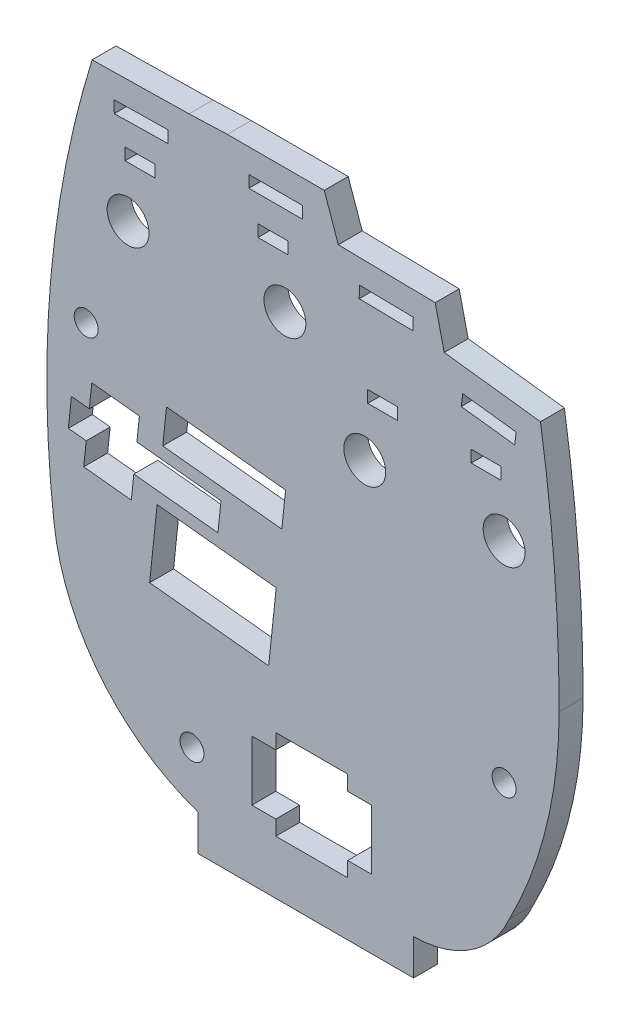
SolidWorks part; units mm, degrees
ref_plane "Front Plane" through (0, 0, 0) normal (0, 0, 1) x (1, 0, 0)
ref_plane "Top Plane" through (0, 0, 0) normal (0, 1, 0) x (1, 0, 0)
ref_plane "Right Plane" through (0, 0, 0) normal (1, 0, 0) x (0, 0, -1)
sketch "Sketch1" plane through (0, 0, 0) normal (0, 0, 1) x (1, 0, 0)
  line L0 (-4.5, 78.51) -> (-4.5, 76.51)
  line L1 (4.5, 78.51) -> (-4.5, 78.51)
  line L2 (-4.5, 76.51) -> (4.5, 76.51)
  line L3 (4.5, 76.51) -> (4.5, 78.51)
  line L4 (-4, -2.5) -> (0, -2.5)
  line L5 (0, 0) -> (18.54, 0) construction
  line L6 (0, 0) -> (0, 82.51) construction
  line L7 (12, 0) -> (0, 0)
  line L8 (0, 0) -> (-22.59, 0) construction
  line L9 (32.6473, 57.3216) -> (37.6473, 57.3216)
  line L10 (-12.9786, -18) -> (-12.9786, -24)
  line L11 (32.6473, 55.3216) -> (37.6473, 55.3216)
  line L12 (37.6473, 55.3216) -> (37.6473, 57.3216)
  line L13 (32.6473, 57.3216) -> (32.6473, 55.3216)
  line L14 (-27.02, 78.0626) -> (-18.0213, 78.2186)
  line L15 (-27.02, 78.0626) -> (-26.9853, 76.0629)
  line L16 (-26.9853, 76.0629) -> (-17.9866, 76.2189)
  line L17 (-17.9866, 76.2189) -> (-18.0213, 78.2186)
  line L18 (15.3631, 57.3216) -> (20.3631, 57.3216)
  line L19 (15.3631, 55.3216) -> (20.3631, 55.3216)
  line L20 (20.3631, 55.3216) -> (20.3631, 57.3216)
  line L21 (15.3631, 57.3216) -> (15.3631, 55.3216)
  line L22 (-2.9786, 72.1512) -> (2.0214, 72.1512)
  line L23 (13.9708, 71.7441) -> (13.9359, 69.7445)
  line L24 (13.9359, 69.7445) -> (22.9346, 69.5874)
  line L25 (-2.9786, 70.1512) -> (2.0214, 70.1512)
  line L26 (22.9695, 71.5871) -> (13.9708, 71.7441)
  line L27 (22.9346, 69.5874) -> (22.9695, 71.5871)
  line L28 (-22.59, 0) -> (-22.59, 82.14) construction
  line L29 (2.0214, 70.1512) -> (2.0214, 72.1512)
  line L30 (28.1404, 69.0671) -> (44.2196, 67.0929)
  line L31 (-2.9786, 72.1512) -> (-2.9786, 70.1512)
  line L32 (40.159, 63.5614) -> (31.226, 64.6582)
  line L33 (1.6326, 35.9121) -> (1.0057, 29.9449)
  line L34 (31.226, 64.6582) -> (30.9823, 62.6731)
  line L35 (-25.179, 72.1512) -> (-20.179, 72.1512)
  line L36 (18.54, 0) -> (18.54, 75.665) construction
  line L37 (0, 0) -> (36.18, 0) construction
  line L38 (-25.179, 70.1512) -> (-20.179, 70.1512)
  line L39 (30.9823, 62.6731) -> (39.9153, 61.5763)
  line L40 (-20.179, 70.1512) -> (-20.179, 72.1512)
  line L41 (-25.179, 72.1512) -> (-25.179, 70.1512)
  line L42 (39.9153, 61.5763) -> (40.159, 63.5614)
  line L43 (1.6326, 35.9121) -> (-18.2579, 38.0017)
  line L44 (0.0654, 20.9942) -> (-1.1883, 9.0599)
  line L45 (12, 0) -> (12, -2.5)
  line L46 (-18.8848, 32.0346) -> (1.0057, 29.9449)
  line L47 (12, -15) -> (0, -15)
  line L48 (-9.666, 24.0728) -> (-9.153, 28.9559)
  line L49 (-34.657, 26.6982) -> (-34.144, 31.5814)
  line L50 (-9.153, 28.9559) -> (-23.2057, 30.4322)
  line L51 (-32.0928, 22.4068) -> (-31.6749, 26.385)
  line L52 (-34.657, 26.6982) -> (-31.6749, 26.385)
  line L53 (-23.7187, 25.5491) -> (-9.666, 24.0728)
  line L54 (-23.2057, 30.4322) -> (-22.7877, 34.4103)
  line L55 (-24.1366, 21.571) -> (-32.0928, 22.4068)
  line L56 (-18.8848, 32.0346) -> (-18.2579, 38.0017)
  line L57 (-30.744, 35.2462) -> (-31.1619, 31.2681)
  line L58 (-22.7877, 34.4103) -> (-30.744, 35.2462)
  line L59 (-31.1619, 31.2681) -> (-34.144, 31.5814)
  line L60 (-24.1366, 21.571) -> (-23.7187, 25.5491)
  line L61 (-19.8251, 23.0838) -> (0.0654, 20.9942)
  line L62 (-21.0789, 11.1495) -> (-1.1883, 9.0599)
  line L63 (0, -15) -> (0, -12.5)
  line L64 (-4, -12.5) -> (-4, -2.5)
  line L65 (-19.8251, 23.0838) -> (-21.0789, 11.1495)
  line L66 (-12.9786, -24) -> (23.0214, -24)
  line L67 (-4, -12.5) -> (0, -12.5)
  line L68 (0, -2.5) -> (0, 0)
  line L69 (16, -12.5) -> (12, -12.5)
  line L70 (16, -12.5) -> (16, -2.5)
  line L71 (16, -2.5) -> (12, -2.5)
  line L72 (12, -12.5) -> (12, -15)
  line L73 (23.0214, -24) -> (23.0214, -18)
  line L74 (36.18, 0) -> (36.18, 68.08) construction
  line L75 (10.4412, 75.8064) -> (26.6388, 75.5236)
  line L76 (-8.1, 82.51) -> (8.1, 82.51)
  line L77 (-14.4912, 82.2805) -> (-30.6888, 81.9995)
  line L78 (28.1404, 69.0671) -> (26.6388, 75.5236)
  line L79 (-9.4095, 26.5144) -> (4.399, 25.0637) construction
  line L80 (39, -7.5) -> (16, -7.5) construction
  line L81 (10.4412, 75.8064) -> (8.1, 82.51)
  line L82 (-8.1, 82.51) -> (-14.4912, 82.2805)
  line L83 (-34.657, 26.6982) -> (47.343, 26.6982) construction
  line L84 (35.6925, 64.1098) -> (36.18, 68.08) construction
  line L85 (38.1473, 11.8216) -> (-37.0527, 11.8216) construction
  line L86 (-18.8848, 32.0346) -> (-19.8251, 23.0838) construction
  line L87 (-19.355, 27.5592) -> (-38.241, 29.5433) construction
  line L88 (18.4702, 71.6656) -> (18.54, 75.665) construction
  line L89 (-22.5206, 78.1406) -> (-22.59, 82.14) construction
  line L90 (0, 78.51) -> (0, 82.51) construction
  line L91 (38.1473, 46.8216) -> (38.1473, 11.8216) construction
  arc A0 (23.0214, -18) -> (39, -7.5) centre (23.0214, -0.592) ccw
  circle A1 centre (38.1473, 11.8216) radius 2
  arc A2 (-37.0527, 11.8216) -> (-30.6888, 81.9995) centre (130.7995, 31.9779) cw
  circle A3 centre (-24.679, 61.6512) radius 3.5
  circle A4 centre (1.5214, 61.6512) radius 3.5
  circle A5 centre (14.8631, 46.8216) radius 3.5
  circle A6 centre (38.1473, 46.8216) radius 3.5
  arc A7 (-37.0527, 11.8216) -> (-12.9786, -18) centre (-1.2138, 16.1253) ccw
  circle A8 centre (-31.6815, 43.4564) radius 2
  circle A9 centre (-14, -9.1244) radius 2
  arc A10 (47.343, 26.6982) -> (39, -7.5) centre (-26.9181, 26.6982) cw
  arc A11 (47.343, 26.6982) -> (44.2196, 67.0929) centre (-215.4276, 26.6982) ccw
  dimension "D1" = 7
  dimension "D15" = 22.59
  dimension "D16" = 82.14
  dimension "D21" = 18
  dimension "D22" = 14.8631
  dimension "D23" = 68.08
  dimension "D24" = 4
  dimension "D27" = 5
  dimension "D28" = 23.0214
  dimension "D29" = 55.3216
  dimension "D30" = 32.6473
  dimension "D39" = 25.179
  dimension "D40" = 9.153
  dimension "D41" = 9.666
  dimension "D42" = 12.9786
  dimension "D43" = 14
  dimension "D44" = 35
  dimension "D47" = 57.3216
  dimension "D48" = 4
  dimension "D65" = 61.6512
  dimension "D72" = 9.1244
  dimension "D61" = 46.8216
  dimension "D62" = 2
  dimension "D53" = 9.0001
  dimension "D2" = 4
  dimension "D8" = 12
  dimension "D14" = 10
  dimension "D9" = 9
  dimension "D10" = 1.0057
  dimension "D11" = 1.5214
  dimension "D12" = 6
  dimension "D13" = 82.51
  dimension "D17" = 18.54
  dimension "D18" = 2.5
  dimension "D19" = 75.665
  dimension "D20" = 36.18
  dimension "D25" = 4
  dimension "D26" = 16.2
  dimension "D32" = 15.3631
  dimension "D33" = 70.1512
  dimension "D34" = 8.1
  dimension "D35" = 38.1473
  dimension "D36" = 2.9786
  dimension "D37" = 4
  dimension "D38" = 4.91
  dimension "D45" = 20
  dimension "D46" = 4
  dimension "D49" = 4.5
  dimension "D50" = 24.679
  dimension "D51" = 25.1285
  dimension "D52" = 31.6815
  dimension "D54" = 8
  dimension "D56" = 14.13
  dimension "D57" = 72.1512
  dimension "D59" = 21.571
  dimension "D60" = 43.4564
  dimension "ThumbLinkLengthMCP" = 18.99
extrude "Boss-Extrude1" add sketch "Sketch1" along normal blind 4
equation "\"D13@Sketch1\"= \"HL@parametersSketch@prostheticParameters.SLDPRT\" * 0.446'Middle Base Frame"
equation "\"D15@Sketch1\"= \"HB@parametersSketch@prostheticParameters.SLDPRT\" * 0.251'Index Base Frame X"
equation "\"D16@Sketch1\"= \"HL@parametersSketch@prostheticParameters.SLDPRT\" * 0.444'Index Base Frame Y"
equation "\"D17@Sketch1\"= \"HB@parametersSketch@prostheticParameters.SLDPRT\" * 0.206'Ring Base Frame X"
equation "\"D19@Sketch1\"= \"HL@parametersSketch@prostheticParameters.SLDPRT\" * 0.409'Ring base Frame Y"
equation "\"D20@Sketch1\"= \"HB@parametersSketch@prostheticParameters.SLDPRT\" * 0.402'Pinky Base Frame X"
equation "\"D23@Sketch1\"= \"HL@parametersSketch@prostheticParameters.SLDPRT\" * 0.368'Pinky Base Frame Y"
equation "\"D26@Sketch1\"= \"fingerWidth@parametersSketch@prostheticParameters.SLDPRT\"'Fingers Width"
equation "\"D59@Sketch1\"= \"HL@parametersSketch@prostheticParameters.SLDPRT\" * 0.1166'Hole Thumb Y"
equation "\"D40@Sketch1\"= \"HB@parametersSketch@prostheticParameters.SLDPRT\" * 0.1017'Hole Thumb X1"
equation "\"D41@Sketch1\"= \"HB@parametersSketch@prostheticParameters.SLDPRT\" * 0.1074'Hole Thumb X2"
equation "\"ThumbLinkLengthMCP@Sketch1\"= \"HB@parametersSketch@prostheticParameters.SLDPRT\" * 0.211"
equation "\"D53@Sketch1\"= \"fingerWidth@parametersSketch@prostheticParameters.SLDPRT\" * 0.55556"
equation "\"D34@Sketch1\"= \"fingerWidth@parametersSketch@prostheticParameters.SLDPRT\" / 2"
